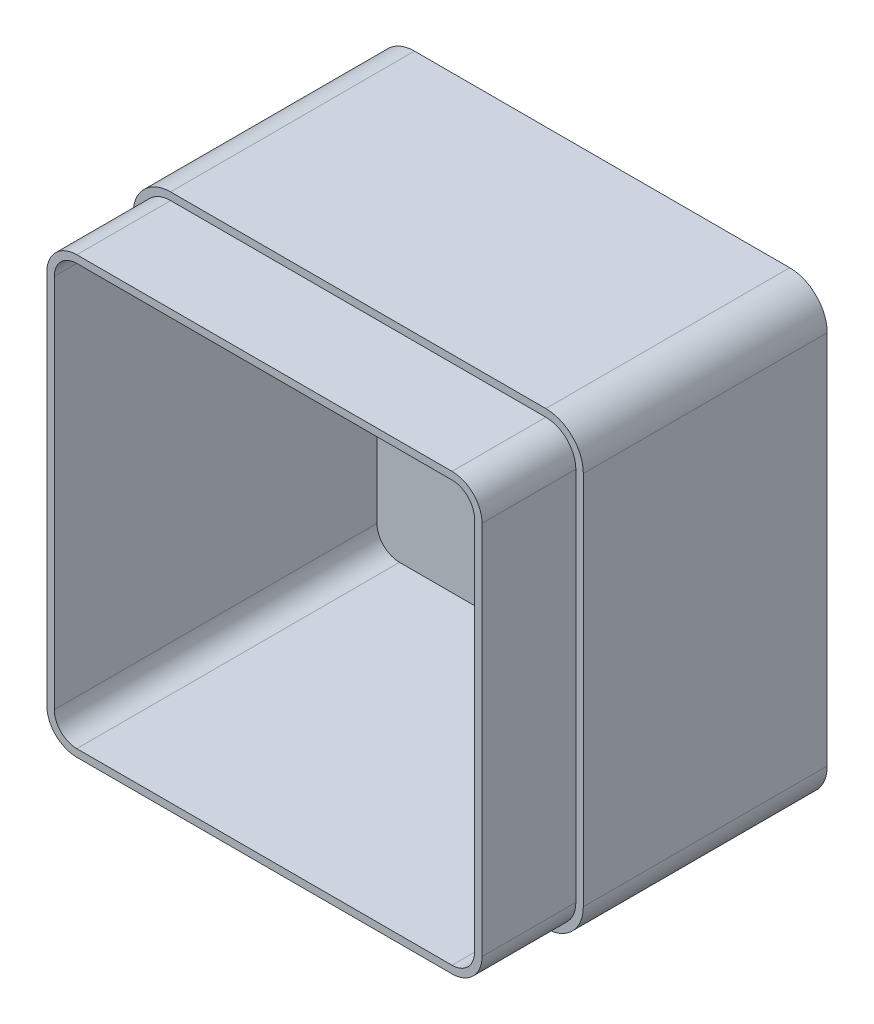
SolidWorks part; units mm, degrees
ref_plane "Front Plane" through (0, 0, 0) normal (0, 0, 1) x (1, 0, 0)
ref_plane "Top Plane" through (0, 0, 0) normal (0, 1, 0) x (1, 0, 0)
ref_plane "Right Plane" through (0, 0, 0) normal (1, 0, 0) x (0, 0, -1)
sketch "Croquis1" plane through (0, 0, 0) normal (0, 0, 1) x (1, 0, 0)
  line L1 (0, 0) -> (120, 0)
  line L2 (0, 0) -> (0, 120)
  line L3 (0, 120) -> (120, 120)
  line L4 (120, 0) -> (120, 120)
  dimension "D1" = 120
  dimension "D2" = 120
extrude "Saliente-Extruir1" add sketch "Croquis1" along normal blind 90
fillet "Redondeo2" radius 10 4 edges at (120, 120, 45) (0, 120, 45) (120, 0, 45) (0, 0, 45)
shell "Vaciado1" thickness 4
sketch "Croquis6" plane through (0, 0, 90) normal (0, 0, 1) x (1, 0, 0)
  line L8 (10, 2) -> (110, 2)
  line L9 (118, 10) -> (118, 110)
  line L10 (110, 118) -> (10, 118)
  line L11 (2, 110) -> (2, 10)
  line L12 (10, 2) -> (110, 2)
  line L13 (118, 10) -> (118, 110)
  line L14 (110, 118) -> (10, 118)
  line L15 (2, 110) -> (2, 10)
  arc A8 (110, 2) -> (118, 10) centre (110, 10) ccw
  arc A9 (118, 110) -> (110, 118) centre (110, 110) ccw
  arc A10 (10, 118) -> (2, 110) centre (10, 110) ccw
  arc A11 (2, 10) -> (10, 2) centre (10, 10) ccw
  arc A12 (110, 2) -> (118, 10) centre (110, 10) ccw
  arc A13 (118, 110) -> (110, 118) centre (110, 110) ccw
  arc A14 (10, 118) -> (2, 110) centre (10, 110) ccw
  arc A15 (2, 10) -> (10, 2) centre (10, 10) ccw
  dimension "D1" = 2
extrude "Cortar-Extruir2" cut sketch "Croquis6" against normal blind 25 flip side to cut
